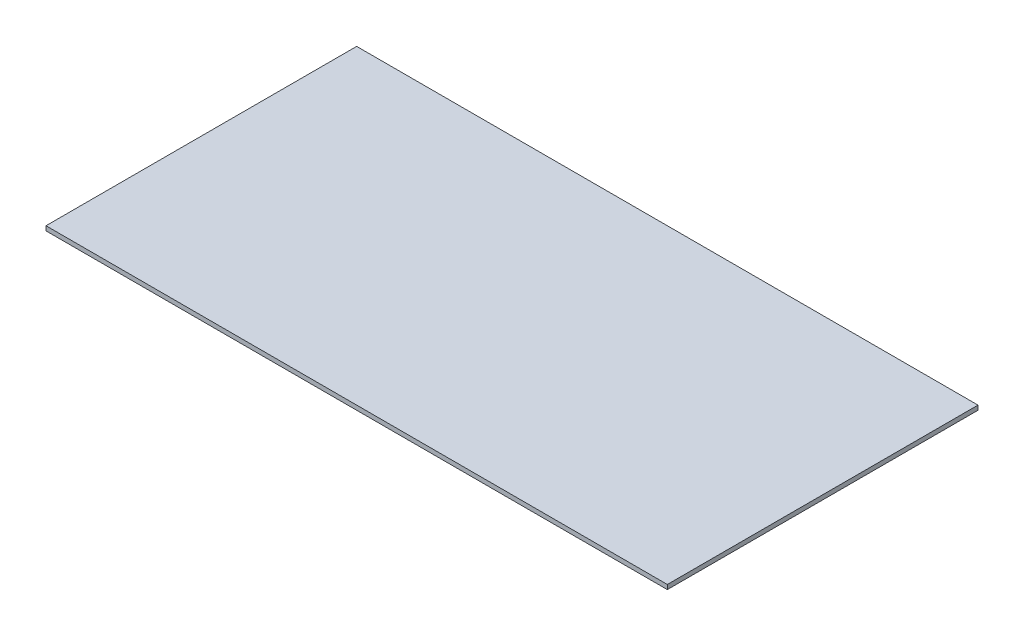
SolidWorks part; units mm, degrees
ref_plane "Front Plane" through (0, 0, 0) normal (0, 0, 1) x (1, 0, 0)
ref_plane "Top Plane" through (0, 0, 0) normal (0, 1, 0) x (1, 0, 0)
ref_plane "Right Plane" through (0, 0, 0) normal (1, 0, 0) x (0, 0, -1)
sketch "Sketch1" plane through (0, 0, 0) normal (0, 1, 0) x (1, 0, 0)
  line L1 (0, 0) -> (50, 0)
  line L2 (0, 0) -> (0, 25)
  line L3 (0, 25) -> (50, 25)
  line L4 (50, 0) -> (50, 25)
  dimension "D1" = 50
  dimension "D2" = 25
extrude "Boss-Extrude1" add sketch "Sketch1" along normal blind 0.36
